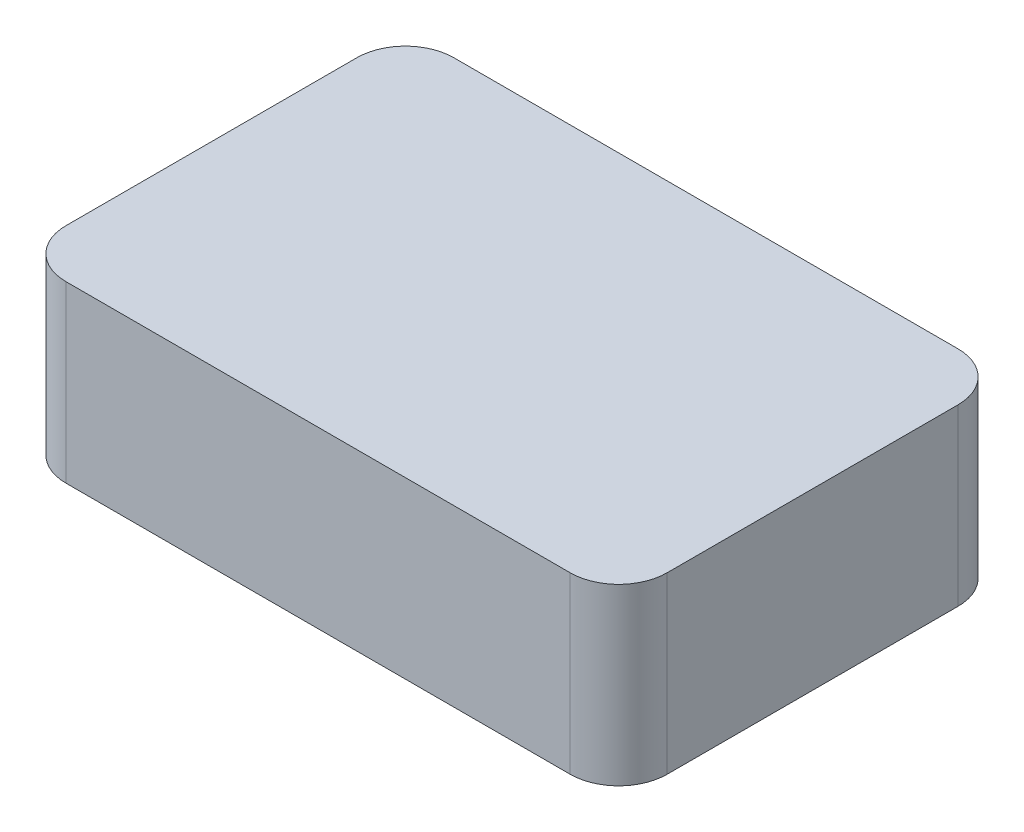
SolidWorks part; units mm, degrees
ref_plane "Front Plane" through (0, 0, 0) normal (0, 0, 1) x (1, 0, 0)
ref_plane "Top Plane" through (0, 0, 0) normal (0, 1, 0) x (1, 0, 0)
ref_plane "Right Plane" through (0, 0, 0) normal (1, 0, 0) x (0, 0, -1)
sketch "Sketch1" plane through (0, 0, 0) normal (0, 1, 0) x (1, 0, 0)
  line L1 (-15.5, -10) -> (15.5, -10)
  line L2 (-15.5, -10) -> (-15.5, 10)
  line L3 (-15.5, 10) -> (15.5, 10)
  line L4 (15.5, -10) -> (15.5, 10)
  line L5 (-15.5, -10) -> (15.5, 10) construction
  line L6 (-15.5, 10) -> (15.5, -10) construction
  point P0 (0, 0)
  dimension "D1" = 31
  dimension "D2" = 20
extrude "Boss-Extrude1" add sketch "Sketch1" along normal mid plane 9
fillet "Fillet1" radius 2.5 4 edges at (-15.5, 0, -10) (15.5, 0, -10) (15.5, 0, 10) (-15.5, 0, 10)
